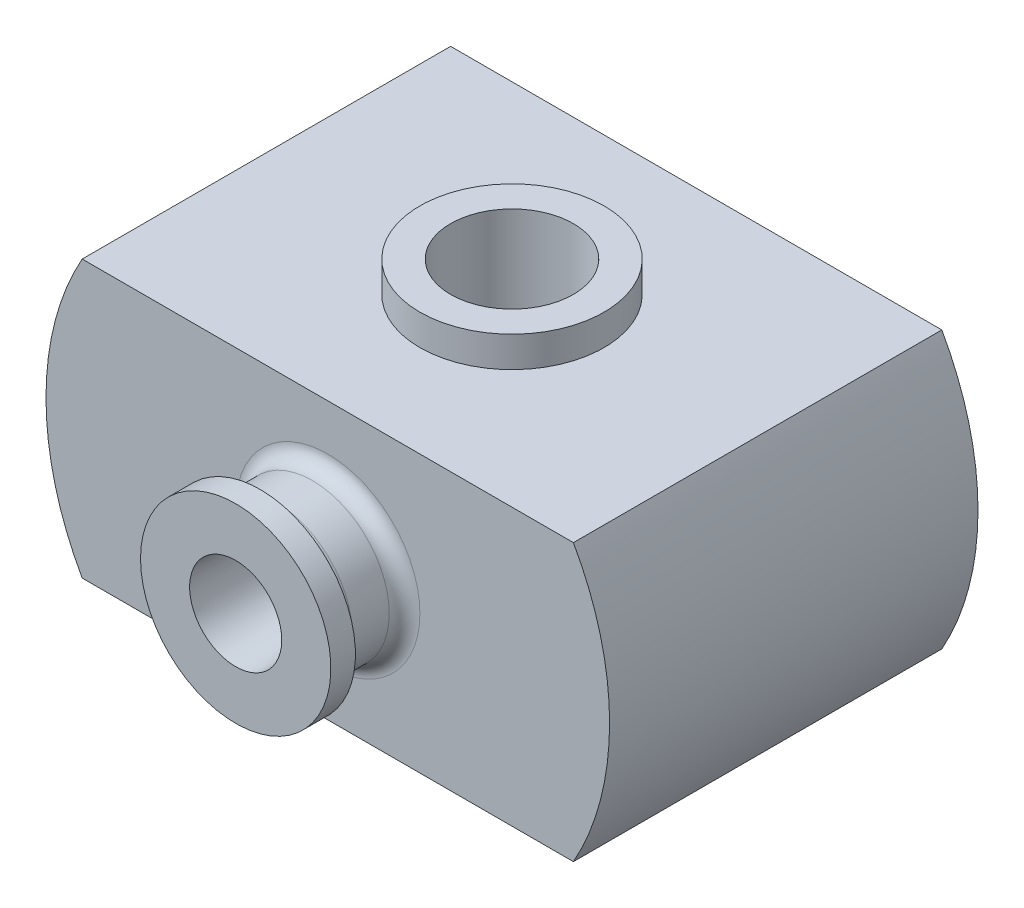
SolidWorks part; units mm, degrees
ref_plane "前视基准面" through (0, 0, 0) normal (0, 0, 1) x (1, 0, 0)
ref_plane "上视基准面" through (0, 0, 0) normal (0, 1, 0) x (1, 0, 0)
ref_plane "右视基准面" through (0, 0, 0) normal (1, 0, 0) x (0, 0, -1)
other "Configuration Table"
sketch "草图1" plane through (0, 0, 0) normal (0, 0, 1) x (1, 0, 0)
  line L1 (-80, 45) -> (80, 45)
  line L3 (-80, -45) -> (80, -45)
  line L5 (-80, 45) -> (80, -45) construction
  line L6 (-80, -45) -> (80, 45) construction
  arc A0 (-80, 45) -> (-80, -45) centre (0, 0) ccw
  arc A1 (80, -45) -> (80, 45) centre (0, 0) ccw
  point P0 (0, 0)
  dimension "D1" = 160
  dimension "D2" = 90
extrude "凸台-拉伸1" add sketch "草图1" along normal blind 120
sketch "草图3" plane through (0, 0, 0) normal (0, 0, -1) x (-1, 0, 0)
  line L1 (-60, 30) -> (60, 30)
  line L3 (-60, -30) -> (60, -30)
  line L5 (-60, 30) -> (60, -30) construction
  line L6 (-60, -30) -> (60, 30) construction
  arc A0 (-60, 30) -> (-60, -30) centre (0, 0) ccw
  arc A1 (60, -30) -> (60, 30) centre (0, 0) ccw
  point P0 (0, 0)
  dimension "D1" = 120
  dimension "D2" = 60
extrude "切除-拉伸1" cut sketch "草图3" against normal blind 114
sketch "草图5" plane through (0, -45, 0) normal (0, -1, 0) x (1, 0, 0)
  line L0 (0, 0) -> (0, 125.1462) construction
  line L1 (-88.4653, 60) -> (96.0693, 60) construction
  circle A0 centre (0, 60) radius 20
  point P5 (0, 60)
extrude "切除-拉伸3" cut sketch "草图5" against normal through all
sketch "草图6" plane through (0, 0, 0) normal (0, 1, 0) x (1, 0, 0)
  circle A0 centre (0, -60) radius 20 construction
  circle A1 centre (0, -60) radius 20
  circle A2 centre (0, -60) radius 30
extrude "凸台-拉伸2" add sketch "草图6" along normal blind 30 from offset 25
mirror "镜向1" about plane through (0, 0, 0) normal (0, 1, 0) of "凸台-拉伸2"
sketch "草图9" plane through (0, 0, 0) normal (0, 1, 0) x (1, 0, 0)
  line L0 (0, 35.7059) -> (0, -149.6916) construction
  line L1 (0, -120) -> (-25, -120)
  line L2 (80, -120) -> (-80, -120) construction
  line L3 (-25, -120) -> (-25, -142)
  line L4 (-25, -142) -> (-31, -142)
  line L5 (-31, -142) -> (-31, -150)
  line L6 (-31, -150) -> (0, -150)
  line L7 (0, -150) -> (0, -120)
  dimension "D1" = 8
  dimension "D2" = 25
  dimension "D3" = 31
  dimension "D4" = 30
revolve "旋转1" add sketch "草图9" angle 360 about L0
fillet "圆角2" radius 5 1 edges at (-25, 0, 120)
fillet "圆角3" radius 5 1 edges at (-25, 0, 142)
sketch "草图10" plane through (0, 0, 0) normal (0, 1, 0) x (1, 0, 0)
  line L0 (0, -161.9396) -> (0, 5.9437) construction
  line L1 (0, -150) -> (-15, -150)
  line L2 (-31, -150) -> (31, -150) construction
  line L3 (-15, -150) -> (-12.5, -105)
  line L4 (-12.5, -105) -> (0, -105)
  line L5 (0, -105) -> (0, -150)
  dimension "D1" = 15
  dimension "D2" = 45
  dimension "D3" = 12.5
revolve "切除-旋转1" cut sketch "草图10" angle 360 about L0
